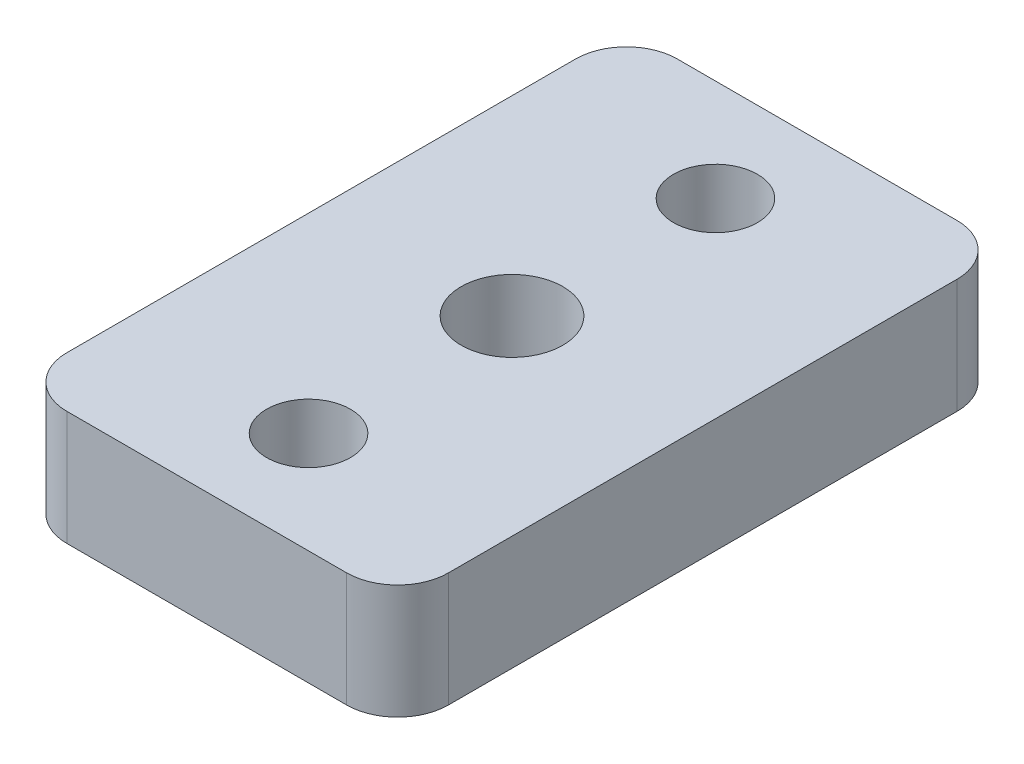
SolidWorks part; units mm, degrees
ref_plane "Front Plane" through (0, 0, 0) normal (0, 0, 1) x (1, 0, 0)
ref_plane "Top Plane" through (0, 0, 0) normal (0, 1, 0) x (1, 0, 0)
ref_plane "Right Plane" through (0, 0, 0) normal (1, 0, 0) x (0, 0, -1)
ref_plane "Plane1" through (0, 4.5, 0) normal (0, 1, 0) x (1, 0, 0)
sketch "Sketch1" plane through (0, 4.5, 0) normal (0, 1, 0) x (1, 0, 0)
  line L0 (5.5, 12) -> (-5.5, 12)
  line L1 (-7.5, 10) -> (-7.5, -10)
  line L2 (-5.5, -12) -> (5.5, -12)
  line L3 (7.5, -10) -> (7.5, 10)
  circle A0 centre (0, 0) radius 2
  circle A1 centre (0, -8) radius 1.65
  circle A2 centre (0, 8) radius 1.65
  arc A3 (-5.5, 12) -> (-7.5, 10) centre (-5.5, 10) ccw
  arc A4 (-7.5, -10) -> (-5.5, -12) centre (-5.5, -10) ccw
  arc A5 (5.5, -12) -> (7.5, -10) centre (5.5, -10) ccw
  arc A6 (7.5, 10) -> (5.5, 12) centre (5.5, 10) ccw
extrude "Boss-Extrude1" add sketch "Sketch1" against normal blind 4.5
